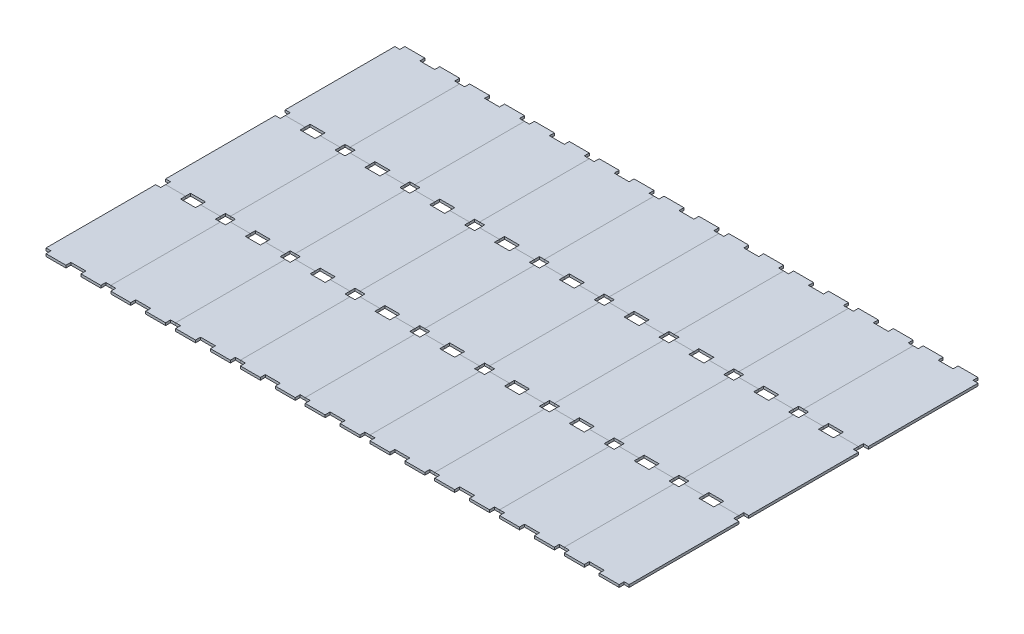
SolidWorks part; units mm, degrees
material "Cedar"
ref_plane "Front Plane" through (0, 0, 0) normal (0, 0, 1) x (1, 0, 0)
ref_plane "Top Plane" through (0, 0, 0) normal (0, 1, 0) x (1, 0, 0)
ref_plane "Right Plane" through (0, 0, 0) normal (1, 0, 0) x (0, 0, -1)
sketch "Sketch1" plane through (0, 0, 0) normal (0, 1, 0) x (1, 0, 0)
  line L1 (-41.275, 76.2) -> (41.275, 76.2)
  line L2 (-41.275, 76.2) -> (-41.275, -76.2)
  line L3 (-41.275, -76.2) -> (41.275, -76.2)
  line L4 (41.275, 76.2) -> (41.275, -76.2)
  line L5 (-41.275, 76.2) -> (41.275, -76.2) construction
  line L6 (-41.275, -76.2) -> (41.275, 76.2) construction
  point P0 (0, 0)
  dimension "D1" = 82.55
  dimension "D2" = 152.4
extrude "Boss-Extrude1" add sketch "Sketch1" along normal blind 3.175
sketch "Sketch2" plane through (0, 3.175, 0) normal (0, 1, 0) x (1, 0, 0)
  line L0 (-41.275, -69.85) -> (41.275, -69.85) construction
  line L1 (-41.275, 76.2) -> (-41.275, -76.2) construction
  line L2 (41.275, -76.2) -> (41.275, 76.2) construction
  line L3 (0, -76.2) -> (0, -69.85) construction
  line L4 (-41.275, -76.2) -> (41.275, -76.2) construction
  line L5 (-34.925, -69.85) -> (-41.275, -69.85)
  line L6 (-34.925, -69.85) -> (-9.525, -69.85) construction
  line L7 (-34.925, -69.85) -> (-34.925, -76.2)
  line L8 (-34.925, -76.2) -> (-9.525, -76.2) construction
  line L9 (-9.525, -69.85) -> (-9.525, -76.2)
  line L10 (-34.925, -69.85) -> (-9.525, -76.2) construction
  line L11 (-34.925, -76.2) -> (-9.525, -69.85) construction
  line L12 (-41.275, -69.85) -> (-41.275, -76.2)
  line L13 (-41.275, -76.2) -> (-34.925, -76.2)
  line L14 (-9.525, -76.2) -> (9.525, -76.2)
  line L15 (0, -76.2) -> (0, -69.85)
  line L16 (9.525, -69.85) -> (-9.525, -69.85)
  line L17 (34.925, -76.2) -> (9.525, -69.85) construction
  line L18 (34.925, -69.85) -> (9.525, -76.2) construction
  line L19 (34.925, -76.2) -> (9.525, -76.2) construction
  line L20 (34.925, -69.85) -> (9.525, -69.85) construction
  line L21 (41.275, -76.2) -> (34.925, -76.2)
  line L22 (41.275, -69.85) -> (41.275, -76.2)
  line L23 (9.525, -69.85) -> (9.525, -76.2)
  line L24 (34.925, -69.85) -> (34.925, -76.2)
  line L25 (34.925, -69.85) -> (41.275, -69.85)
  point P10 (-22.225, -73.025)
  point P22 (22.225, -73.025)
  line M12 (41.275, -76.2) -> (41.275, 76.2)
  line M14 (-41.275, 76.2) -> (-41.275, -76.2)
  line M15 (-41.275, -76.2) -> (41.275, -76.2)
  dimension "D1" = 6.35
  dimension "D2" = 9.525
  dimension "D3" = 25.4
extrude "Cut-Extrude1" cut sketch "Sketch2" against normal through all contours L7 L5 M14 M15 | L15 L16 L9 M15 | L23 L16 L15 L14 | L25 L24 M15 M12
mirror "Mirror1" about plane through (0, 0, 0) normal (0, 0, 1) of "Cut-Extrude1"
pattern_linear "LPattern1" count 9 spacing 82.55 along (1, 0, 0) count 3 spacing 152.4 along (0, 0, 1) of bodies 103
